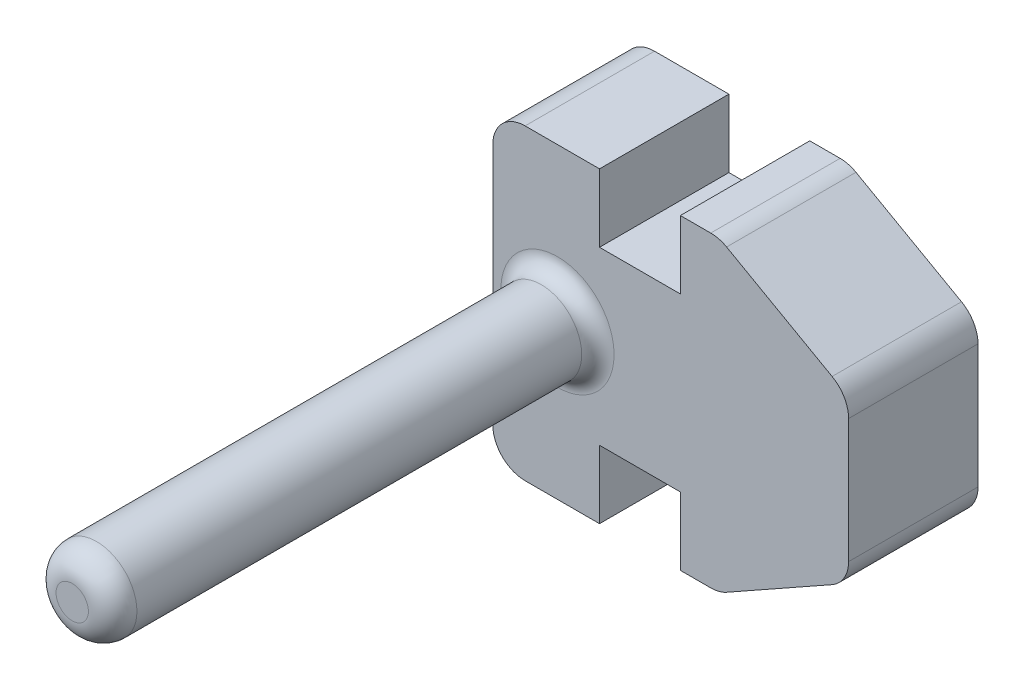
SolidWorks part; units mm, degrees
ref_plane "Front Plane" through (0, 0, 0) normal (0, 0, 1) x (1, 0, 0)
ref_plane "Top Plane" through (0, 0, 0) normal (0, 1, 0) x (1, 0, 0)
ref_plane "Right Plane" through (0, 0, 0) normal (1, 0, 0) x (0, 0, -1)
sketch "Sketch1" plane through (0, 0, 0) normal (0, 0, 1) x (1, 0, 0)
  line L1 (3.5, -4.75) -> (-3.5, -4.75)
  line L2 (3.5, -4.75) -> (3.5, 4.75)
  line L3 (3.5, 4.75) -> (-3.5, 4.75)
  line L4 (-3.5, -4.75) -> (-3.5, 4.75)
  line L5 (3.5, -4.75) -> (-3.5, 4.75) construction
  line L6 (3.5, 4.75) -> (-3.5, -4.75) construction
  line L7 (-0.2, 4.75) -> (2.3, 4.75)
  line L8 (-0.2, 4.75) -> (-0.2, 2.65)
  line L9 (-0.2, 2.65) -> (2.3, 2.65)
  line L10 (2.3, 4.75) -> (2.3, 2.65)
  line L11 (-0.2, -4.75) -> (2.3, -4.75)
  line L12 (-0.2, -4.75) -> (-0.2, -2.65)
  line L13 (-0.2, -2.65) -> (2.3, -2.65)
  line L14 (2.3, -4.75) -> (2.3, -2.65)
  point P0 (0, 0)
  dimension "D1" = 7
  dimension "D2" = 9.5
  dimension "D3" = 2.1
  dimension "D4" = 2.1
  dimension "D5" = 2.5
  dimension "D6" = 2.5
  dimension "D7" = 3.3
  dimension "D8" = 3.3
extrude "Boss-Extrude1" add sketch "Sketch1" along normal blind 4 contours L14 L1 L2 L3 L10 L9 L8 L4 L12 L13
sketch "Sketch2" plane through (0, 0, 0) normal (0, 0, -1) x (-1, 0, 0)
  line L0 (-3.5, 4.75) -> (-7.5, 2.5)
  line L1 (-7.5, 2.5) -> (-7.5, -2.5)
  line L2 (-7.5, -2.5) -> (-3.5, -4.75)
  line L12 (-2.3, -4.75) -> (-2.3, -2.65)
  line L13 (-2.3, -2.65) -> (0.2, -2.65)
  line L14 (0.2, -2.65) -> (0.2, -4.75)
  line L15 (0.2, -4.75) -> (3.5, -4.75)
  line L16 (3.5, -4.75) -> (3.5, 4.75)
  line L17 (3.5, 4.75) -> (0.2, 4.75)
  line L18 (0.2, 4.75) -> (0.2, 2.65)
  line L19 (0.2, 2.65) -> (-2.3, 2.65)
  line L20 (-2.3, 2.65) -> (-2.3, 4.75)
  line L21 (-2.3, 4.75) -> (-3.5, 4.75)
  line L22 (-3.5, 4.75) -> (-3.5, -4.75)
  line L23 (-3.5, -4.75) -> (-2.3, -4.75)
  line L24 (-2.3, -4.75) -> (-2.3, -2.65)
  line L25 (-2.3, -2.65) -> (0.2, -2.65)
  line L26 (0.2, -2.65) -> (0.2, -4.75)
  line L27 (0.2, -4.75) -> (3.5, -4.75)
  line L28 (3.5, -4.75) -> (3.5, 4.75)
  line L29 (3.5, 4.75) -> (0.2, 4.75)
  line L30 (0.2, 4.75) -> (0.2, 2.65)
  line L31 (0.2, 2.65) -> (-2.3, 2.65)
  line L32 (-2.3, 2.65) -> (-2.3, 4.75)
  line L33 (-2.3, 4.75) -> (-3.5, 4.75)
  line L34 (-3.5, 4.75) -> (-3.5, -4.75)
  line L35 (-3.5, -4.75) -> (-2.3, -4.75)
  line M23 (-3.5, 4.75) -> (-3.5, -4.75)
  dimension "D2" = 5
  dimension "D3" = 4
  dimension "D4" = 2.25
  dimension "D1" = 0
extrude "Boss-Extrude2" add sketch "Sketch2" against normal blind 4 contours L1 L2 L0 M23
sketch "Sketch3" plane through (0, 0, 4) normal (0, 0, 1) x (1, 0, 0)
  line L12 (3.5, -4.75) -> (7.5, -2.5)
  line L14 (2.3, -2.65) -> (2.3, -4.75)
  line L15 (2.3, -4.75) -> (3.5, -4.75)
  line L18 (3.5, -4.75) -> (7.5, -2.5)
  line L19 (3.5, 4.75) -> (2.3, 4.75)
  line L20 (2.3, 4.75) -> (2.3, 2.65)
  line L21 (2.3, 2.65) -> (-0.2, 2.65)
  line L22 (-0.2, 2.65) -> (-0.2, 4.75)
  line L23 (-0.2, 4.75) -> (-3.5, 4.75)
  line L24 (-3.5, 4.75) -> (-3.5, -4.75)
  line L25 (-3.5, -4.75) -> (-0.2, -4.75)
  line L26 (-0.2, -4.75) -> (-0.2, -2.65)
  line L27 (-0.2, -2.65) -> (2.3, -2.65)
  line L28 (2.3, -2.65) -> (2.3, -4.75)
  line L29 (2.3, -4.75) -> (3.5, -4.75)
  line L33 (3.5, 4.75) -> (2.3, 4.75)
  line L34 (2.3, 4.75) -> (2.3, 2.65)
  line L35 (2.3, 2.65) -> (-0.2, 2.65)
  line L36 (-0.2, 2.65) -> (-0.2, 4.75)
  line L37 (-0.2, 4.75) -> (-3.5, 4.75)
  line L38 (-3.5, 4.75) -> (-3.5, -4.75)
  line L39 (-3.5, -4.75) -> (-0.2, -4.75)
  line L40 (-0.2, -4.75) -> (-0.2, -2.65)
  line L41 (-0.2, -2.65) -> (2.3, -2.65)
  line L42 (7.5, -2.5) -> (7.5, 2.5)
  line L43 (7.5, -2.5) -> (7.5, 2.5)
  line L44 (7.5, 2.5) -> (3.5, 4.75)
  line L45 (7.5, 2.5) -> (3.5, 4.75)
  circle A0 centre (-1.5, 0) radius 1.25
  dimension "D2" = 2.5
  dimension "D3" = 2
  dimension "D4" = 4.75
  dimension "D1" = 0
extrude "Boss-Extrude3" add sketch "Sketch3" along normal blind 15 contours A0
fillet "Fillet1" radius 1 6 edges at (3.5, 4.75, 2) (7.5, 2.5, 2) (7.5, -2.5, 2) (3.5, -4.75, 2) (-3.5, -4.75, 2) (-3.5, 4.75, 2)
fillet "Fillet2" radius 0.5 1 edges at (-0.25, 0, 4)
fillet "Fillet3" radius 0.75 1 edges at (-0.25, 0, 19)
